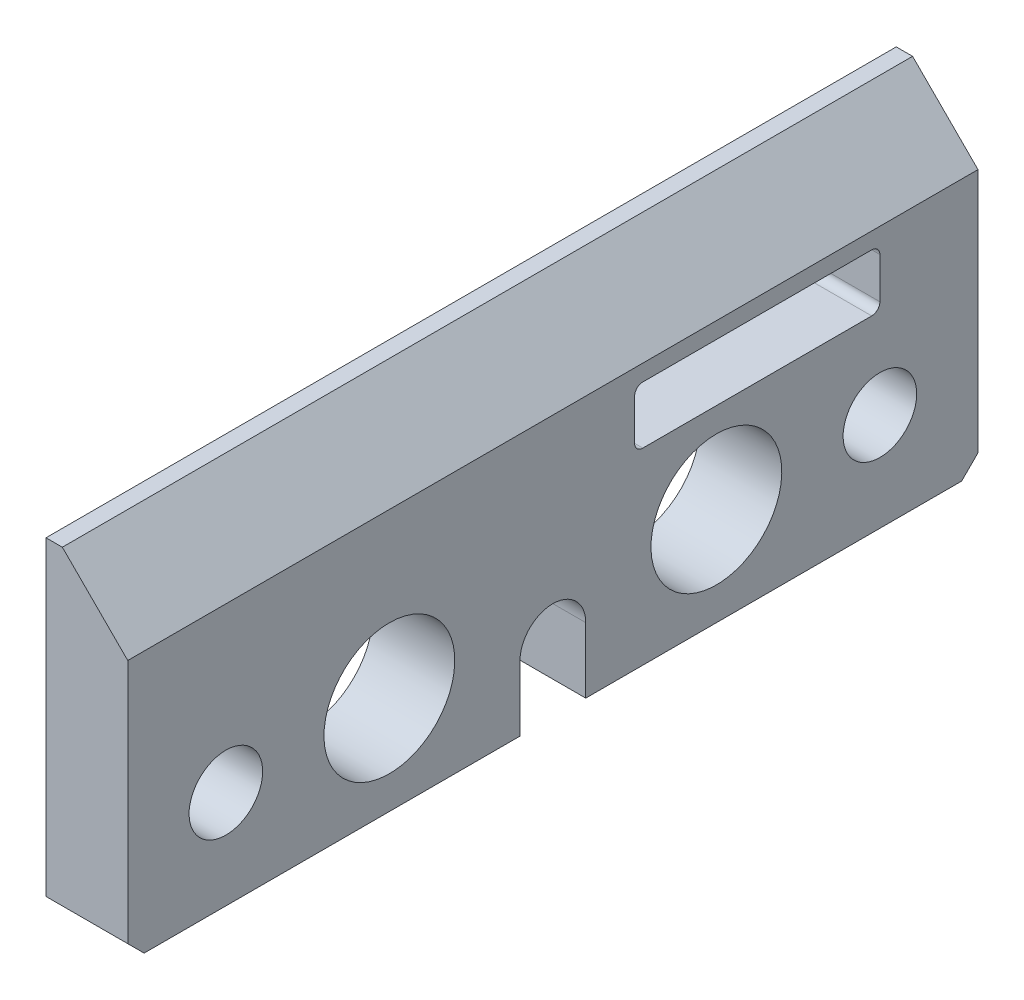
SolidWorks part; units mm, degrees
ref_plane "Front Plane" through (0, 0, 0) normal (0, 0, 1) x (1, 0, 0)
ref_plane "Top Plane" through (0, 0, 0) normal (0, 1, 0) x (1, 0, 0)
ref_plane "Right Plane" through (0, 0, 0) normal (1, 0, 0) x (0, 0, -1)
sketch "Sketch1" plane through (0, 0, 0) normal (0, 0, 1) x (1, 0, 0)
  line L1 (-0.828, 3.4236) -> (4.172, 3.4236)
  line L2 (-0.828, 3.4236) -> (-0.828, -16.5764)
  line L3 (-0.828, -16.5764) -> (4.172, -16.5764)
  line L4 (4.172, 3.4236) -> (4.172, -16.5764)
  dimension "D1" = 5
  dimension "D2" = 20
extrude "Boss-Extrude1" add sketch "Sketch1" along normal blind 52
sketch "Sketch2" plane through (4.172, 0, 0) normal (1, 0, 0) x (0, 0, -1)
  line L0 (-52, -16.5764) -> (0, -16.5764) construction
  line L1 (-23.99, -16.5764) -> (-28.01, -16.5764)
  line L2 (-23.99, -16.5764) -> (-23.99, -12.5764)
  line L4 (-28.01, -16.5764) -> (-28.01, -12.5764)
  line L5 (-52, -16.5764) -> (-52, 3.4236) construction
  line L6 (-21, -1.5764) -> (-6, -1.5764)
  line L7 (-21, -1.5764) -> (-21, -5.0764)
  line L8 (-21, -5.0764) -> (-6, -5.0764)
  line L9 (-6, -1.5764) -> (-6, -5.0764)
  circle A0 centre (-46, -10.5764) radius 2.25
  circle A1 centre (-36, -10.5764) radius 4
  circle A2 centre (-16, -10.5764) radius 4
  circle A3 centre (-6, -10.5764) radius 2.25
  arc A4 (-23.99, -12.5764) -> (-28.01, -12.5764) centre (-26, -12.5764) ccw
  point P22 (-21, -3.3264)
  dimension "D8" = 4.5
  dimension "D9" = 8
  dimension "D1" = 6
  dimension "D2" = 6
  dimension "D3" = 16
  dimension "D5" = 4.02
  dimension "D6" = 36
  dimension "D7" = 46
  dimension "D11" = 31
  dimension "D12" = 46
  dimension "D13" = 3.5
  dimension "D14" = 11.5
extrude "Cut-Extrude1" cut sketch "Sketch2" against normal blind 52
fillet "Fillet1" radius 0.5 4 edges at (1.672, -5.0764, 6) (1.672, -1.5764, 6) (1.672, -5.0764, 21) (1.672, -1.5764, 21)
chamfer "Chamfer1" distance 1 angle 45 2 edges at (1.672, -16.5764, 0) (1.672, -16.5764, 52)
chamfer "Chamfer2" distance 4 angle 45 1 edges at (4.172, 3.4236, 26)
